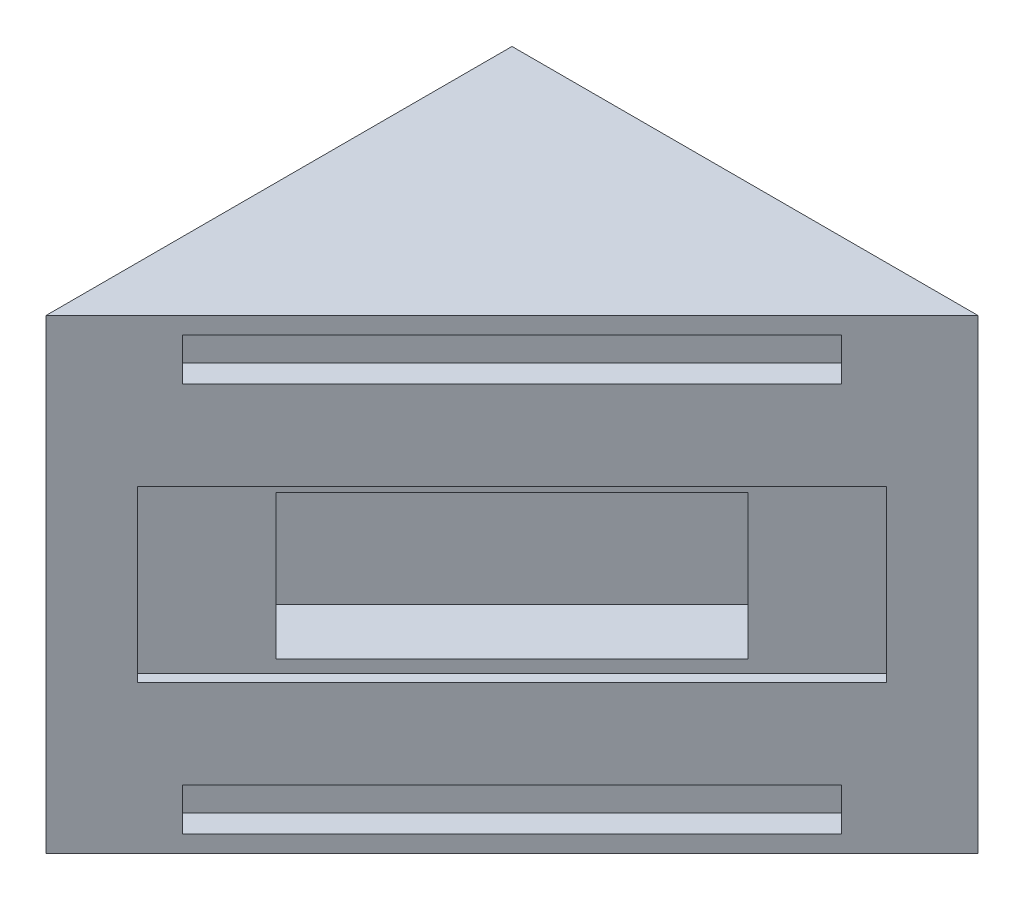
SolidWorks part; units mm, degrees
ref_plane "Front Plane" through (0, 0, 0) normal (0, 0, 1) x (1, 0, 0)
ref_plane "Top Plane" through (0, 0, 0) normal (0, 1, 0) x (1, 0, 0)
ref_plane "Right Plane" through (0, 0, 0) normal (1, 0, 0) x (0, 0, -1)
sketch "Sketch1" plane through (0, 0, 0) normal (0, 1, 0) x (1, 0, 0)
  line L1 (0, 0) -> (69.85, 0)
  line L2 (0, 0) -> (0, 69.85)
  line L3 (0, 69.85) -> (69.85, 69.85)
  line L4 (69.85, 0) -> (69.85, 69.85)
  dimension "D1" = 69.85
  dimension "D2" = 69.85
extrude "Boss-Extrude1" add sketch "Sketch1" along normal blind 69.85
ref_plane "Plane1" through (0, 0, 0) normal (0.7071, 0, 0.7071) x (0.7071, 0, -0.7071)
sketch "Sketch2" plane through (0, 0, 0) normal (0.7071, 0, 0.7071) x (0.7071, 0, -0.7071)
  line L0 (98.7828, 69.85) -> (98.7828, 0) construction
  line L1 (98.7828, 0) -> (49.3914, 0) construction
  line L2 (49.3914, 0) -> (0, 0) construction
  line L3 (0, 69.85) -> (0, 0) construction
  line L4 (49.3914, 69.85) -> (0, 69.85) construction
  line L5 (98.7828, 69.85) -> (49.3914, 69.85) construction
  line L6 (98.7828, 69.85) -> (98.7828, 0)
  line L7 (98.7828, 0) -> (49.3914, 0)
  line L8 (49.3914, 0) -> (0, 0)
  line L9 (0, 69.85) -> (0, 0)
  line L10 (49.3914, 69.85) -> (0, 69.85)
  line L11 (98.7828, 69.85) -> (49.3914, 69.85)
extrude "Cut-Extrude2" cut sketch "Sketch2" along normal blind 100
surface "Surface-Knit1"
sketch "Sketch3" plane through (0, 0, 0) normal (0.7071, 0, 0.7071) x (0.7071, 0, -0.7071)
  line L0 (14.4664, 8.89) -> (84.3164, 8.89)
  line L1 (14.4664, 67.31) -> (84.3164, 67.31)
  line L2 (14.4664, 67.31) -> (14.4664, 60.96)
  line L3 (14.4664, 60.96) -> (84.3164, 60.96)
  line L4 (0, 0) -> (98.7828, 0) construction
  line L20 (84.3164, 67.31) -> (84.3164, 60.96)
  line L21 (14.4664, 8.89) -> (14.4664, 2.54)
  line L22 (14.4664, 2.54) -> (84.3164, 2.54)
  line L23 (84.3164, 8.89) -> (84.3164, 2.54)
  line L28 (98.7828, 69.85) -> (0, 69.85) construction
  point P8 (49.3914, 2.54)
  point P9 (49.3914, 60.96)
  dimension "D1" = 6.35
  dimension "D2" = 2.54
  dimension "D3" = 69.85
  dimension "D4" = 6.35
  dimension "D5" = 2.54
  dimension "D6" = 69.85
extrude "Cut-Extrude4" cut sketch "Sketch3" against normal blind 3.81
sketch "Sketch4" plane through (0, 0, 0) normal (0.7071, 0, 0.7071) x (0.7071, 0, -0.7071)
  line L0 (0, 69.85) -> (98.7828, 0) construction
  line L1 (98.7828, 69.85) -> (0, 0) construction
  line L2 (9.7039, 47.625) -> (89.0789, 22.225) construction
  line L3 (89.0789, 47.625) -> (9.7039, 22.225) construction
  line L12 (9.7039, 22.225) -> (89.0789, 22.225)
  line L13 (89.0789, 22.225) -> (89.0789, 47.625)
  line L14 (89.0789, 47.625) -> (9.7039, 47.625)
  line L15 (9.7039, 47.625) -> (9.7039, 22.225)
  point P4 (49.3914, 34.925)
  point P5 (49.3914, 34.925)
  point P7 (0, 0)
  point P9 (0, 0)
  point P17 (0, 0)
  point P19 (0, 0)
  point P20 (0, 0)
  dimension "D1" = 79.375
  dimension "D2" = 25.4
extrude "Cut-Extrude5" cut sketch "Sketch4" against normal blind 1.6
sketch "Sketch5" plane through (-1.1314, 0, -1.1314) normal (0.7071, 0, 0.7071) x (0.7071, 0, -0.7071)
  line L0 (0, 69.85) -> (98.7828, 0) construction
  line L1 (0, 0) -> (98.7828, 0) construction
  line L2 (98.7828, 69.85) -> (98.7828, 0) construction
  line L3 (98.7828, 69.85) -> (0, 0) construction
  line L5 (24.3914, 45.72) -> (74.3914, 45.72)
  line L6 (24.3914, 45.72) -> (24.3914, 24.13)
  line L7 (24.3914, 24.13) -> (74.3914, 24.13)
  line L8 (74.3914, 45.72) -> (74.3914, 24.13)
  line L9 (24.3914, 45.72) -> (74.3914, 24.13) construction
  line L10 (24.3914, 24.13) -> (74.3914, 45.72) construction
  point P11 (49.3914, 34.925)
  dimension "D1" = 50
  dimension "D2" = 21.59
extrude "Cut-Extrude6" cut sketch "Sketch5" against normal blind 10
